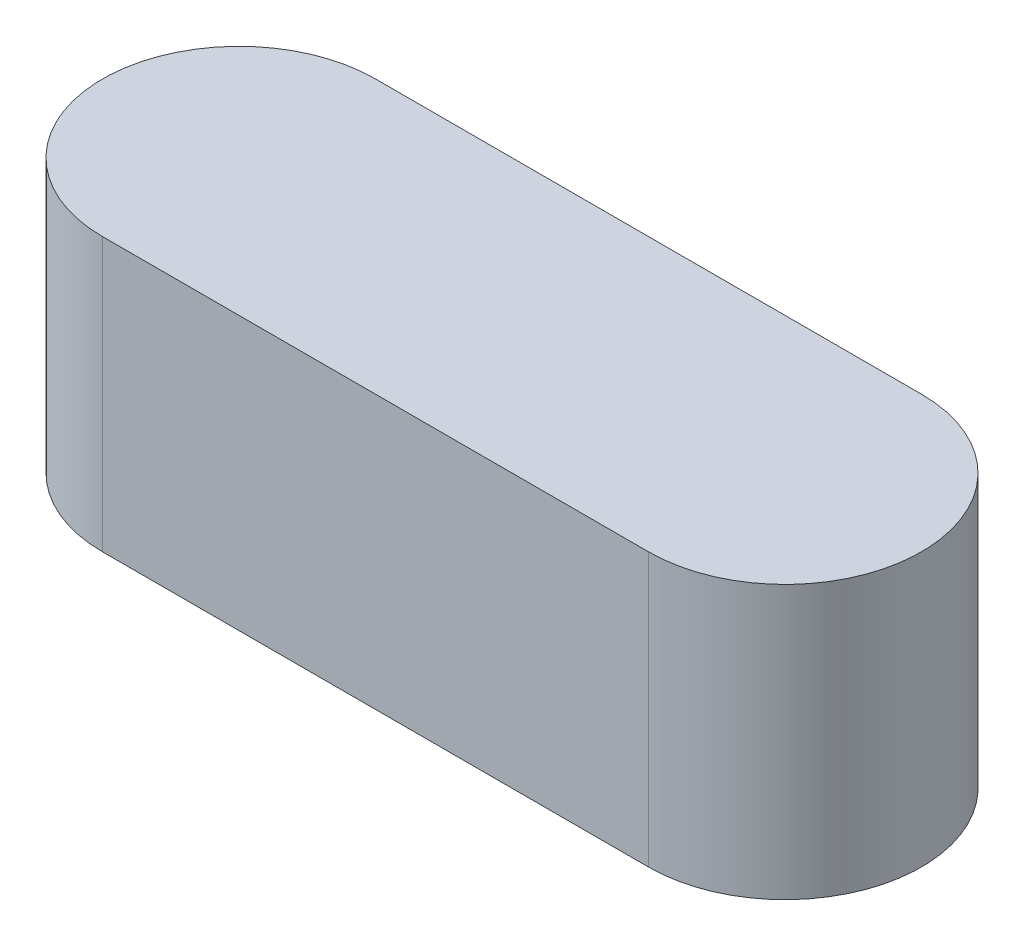
SolidWorks part; units mm, degrees
ref_plane "Front" through (0, 0, 0) normal (0, 0, 1) x (1, 0, 0)
ref_plane "Top" through (0, 0, 0) normal (0, 1, 0) x (1, 0, 0)
ref_plane "Right" through (0, 0, 0) normal (1, 0, 0) x (0, 0, -1)
sketch "support-front-body" plane through (0, 0, 0) normal (0, 0, 1) x (1, 0, 0)
  line L0 (-3, 1) -> (3, 1) construction
  line L1 (-3, 2) -> (3, 2)
  line L2 (-3, 2) -> (-3, 0)
  line L3 (-3, 0) -> (3, 0)
  line L4 (3, 2) -> (3, 0)
  line L5 (0, 2) -> (0, 0) construction
  dimension "length" = 6
  dimension "height" = 2
sketch "support-top-body" plane through (0, 0, 0) normal (0, 1, 0) x (1, 0, 0)
  line L0 (-2, 1) -> (2, 1)
  line L1 (2, -1) -> (-2, -1)
  line L2 (2, 0) -> (-2, 0) construction
  line L3 (0, 1) -> (0, -1) construction
  line L4 (-3, 0) -> (3, 0) construction
  line L5 (2, 0) -> (3, 0) construction
  line L6 (-2, 0) -> (-3, 0) construction
  arc A0 (2, 1) -> (2, -1) centre (2, 0) cw
  arc A1 (-2, -1) -> (-2, 1) centre (-2, 0) cw
  dimension "width" = 2
ref_plane "ref-plane-top" through (0, 2, 0) normal (0, 1, 0) x (-1, 0, 0)
sketch "Sketch4" plane through (0, 0, 0) normal (0, 1, 0) x (1, 0, 0)
  line L2 (2, 1) -> (-2, 1)
  line L3 (-2, -1) -> (2, -1)
  line L4 (2, 1) -> (-2, 1)
  line L5 (-2, -1) -> (2, -1)
  arc A2 (-2, 1) -> (-2, -1) centre (-2, 0) ccw
  arc A3 (2, -1) -> (2, 1) centre (2, 0) ccw
  arc A4 (-2, 1) -> (-2, -1) centre (-2, 0) ccw
  arc A5 (2, -1) -> (2, 1) centre (2, 0) ccw
  dimension "D1" = 0
extrude "body" add sketch "Sketch4" along normal up to surface (2 mm away) up to plane "ref-plane-top"
